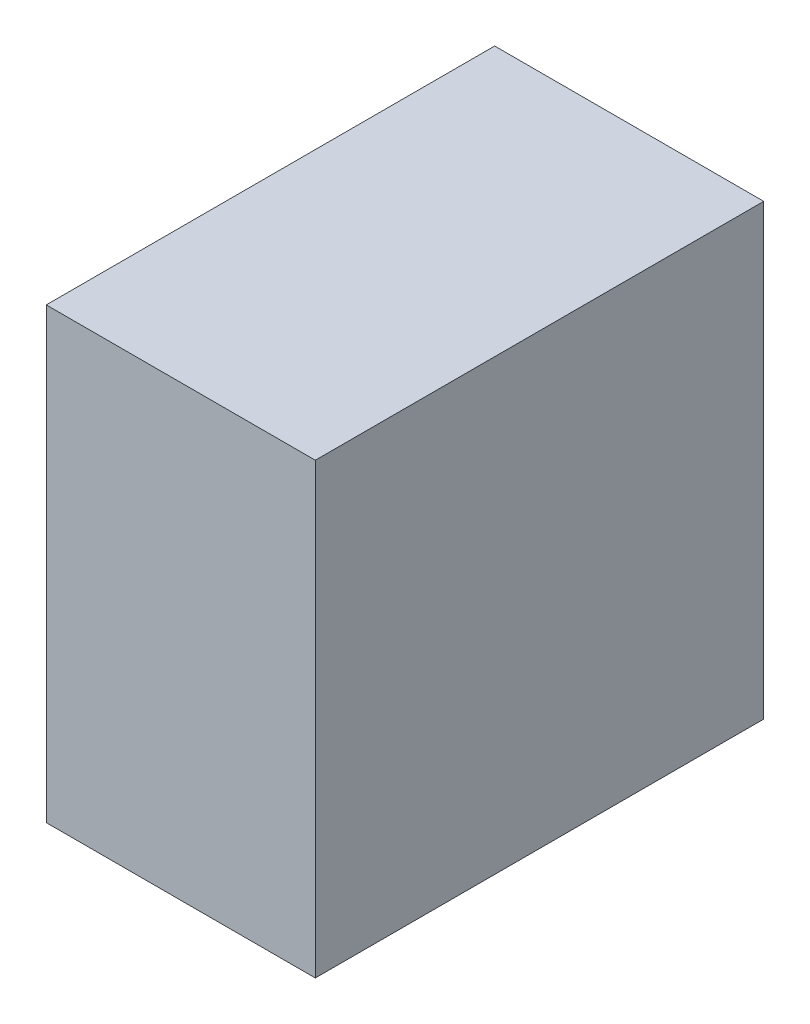
SolidWorks part; units mm, degrees
ref_plane "Front Plane" through (0, 0, 0) normal (0, 0, 1) x (1, 0, 0)
ref_plane "Top Plane" through (0, 0, 0) normal (0, 1, 0) x (1, 0, 0)
ref_plane "Right Plane" through (0, 0, 0) normal (1, 0, 0) x (0, 0, -1)
sketch "Sketch1" plane through (0, 0, 0) normal (1, 0, 0) x (0, 0, -1)
  line L1 (-25, 25) -> (25, 25)
  line L2 (-25, 25) -> (-25, -25)
  line L3 (-25, -25) -> (25, -25)
  line L4 (25, 25) -> (25, -25)
  line L5 (-25, 25) -> (25, -25) construction
  line L6 (-25, -25) -> (25, 25) construction
  point P0 (0, 0)
  dimension "D1" = 50
  dimension "D2" = 50
extrude "Boss-Extrude1" add sketch "Sketch1" along normal blind 30
